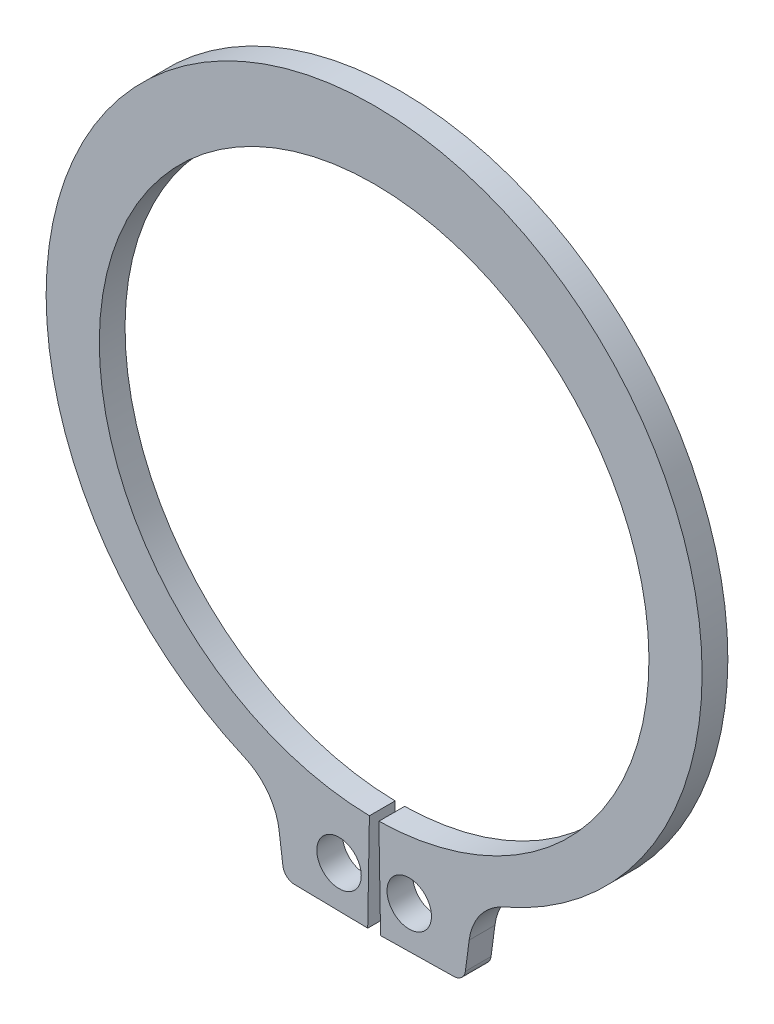
SolidWorks part; units mm, degrees
ref_plane "Plane1" through (0, 0, 0) normal (0, 0, 1) x (1, 0, 0)
ref_plane "Plane2" through (0, 0, 0) normal (0, 1, 0) x (1, 0, 0)
ref_plane "Plane3" through (0, 0, 0) normal (1, 0, 0) x (0, 0, -1)
sketch "Clipboard" plane through (0, 0, 0) normal (0, 0, 1) x (1, 0, 0)
  line L0 (0, 0) -> (2.9, 0)
  line L1 (0, 0) -> (0, 1.7)
  line L2 (0, 0) -> (0, -4.2)
  circle A0 centre (0, 0) radius 0.95
  circle A1 centre (0, 0) radius 12.5
  dimension "HoleDia" = 1.9
  dimension "ShaftDia" = 25
  dimension "LargeSection" = 2.9
  dimension "SmallSection" = 1.7
  dimension "LugSection" = 4.2
sketch "BodySke" plane through (0, 0, 0) normal (0, 0, 1) x (1, 0, 0)
  line L0 (-1.5431, 0) -> (1.5431, 0) construction
  line L1 (0, 0) -> (0, 14.65) construction
  line L2 (0.2026, -11.7483) -> (0.275, -15.9476)
  line L3 (-0.2026, -11.7483) -> (-0.275, -15.9476)
  line L4 (0, 0) -> (6.5413, -14.547) construction
  line L5 (0, 0) -> (-6.5413, -14.547) construction
  line L6 (0.275, -15.9476) -> (3.4129, -15.8935)
  line L7 (4.063, -14.2207) -> (3.9, -15.4589)
  line L8 (-4.063, -14.2207) -> (-3.9, -15.4589)
  line L9 (-0.275, -15.9476) -> (-3.4129, -15.8935)
  circle A0 centre (0, 0) radius 11.75 construction
  arc A1 (0.2026, -11.7483) -> (-0.2026, -11.7483) centre (0, 0) ccw
  arc A2 (5.516, -12.2669) -> (-5.516, -12.2669) centre (0, 0.6264) ccw construction
  arc A3 (0.275, -15.9476) -> (3.9942, -15.4418) centre (0, 0) ccw construction
  arc A4 (5.5517, -12.2515) -> (4.063, -14.2207) centre (6.5413, -14.547) ccw
  arc A5 (-4.063, -14.2207) -> (-5.5517, -12.2515) centre (-6.5413, -14.547) ccw
  arc A6 (-3.9942, -15.4418) -> (-0.275, -15.9476) centre (0, 0) ccw construction
  arc A7 (5.5517, -12.2515) -> (-5.5517, -12.2515) centre (0, 0.6264) ccw
  arc A8 (-4.1437, -13.6081) -> (4.1437, -13.6081) centre (0, 0) ccw construction
  circle A9 centre (1.5, -14.1457) radius 0.95
  circle A10 centre (-1.5, -14.1457) radius 0.95
  arc A11 (3.9, -15.4589) -> (3.4129, -15.8935) centre (3.4043, -15.3936) cw
  arc A12 (-3.9, -15.4589) -> (-3.4129, -15.8935) centre (-3.4043, -15.3936) ccw
  point P28 (3.8991, -15.4661)
  point P31 (-3.8991, -15.4661)
  dimension "GrooveDia" = 23.5
  dimension "LugRad" = 15.95
  dimension "HoleOffsetRad" = 14.225
  dimension "HoleDia" = 1.9
  dimension "D3" = 0.5
  dimension "LargeRad" = 14.65
  dimension "SmallRad" = 13.45
  dimension "SmallAngle" = 48.424
  dimension "D2" = 15
  dimension "HoleSpacing" = 3
  dimension "Gap" = 0.55
extrude "Body" add sketch "BodySke" against normal blind 1.1
sketch "NotSke" plane through (0, 0, 0) normal (0, 0, 1) x (1, 0, 0)
  line L0 (1.5, -13.1957) -> (1.5, -15.0957)
  line L1 (1.5, -15.0957) -> (-1.5, -15.0957)
  line L2 (-1.5, -15.0957) -> (-1.5, -13.1957)
  line L3 (-1.5, -13.1957) -> (1.5, -13.1957)
  circle A0 centre (1.5, -14.1457) radius 0.95 construction
  circle A1 centre (-1.5, -14.1457) radius 0.95 construction
extrude "Notch" [suppressed] cut sketch "NotSke" against normal through all
equation "' \"ShaftDia@Clipboard\" = 4"
equation "' \"Thickness@Body\" = 0.25"
equation "' \"GrooveDia@BodySke\" = 3.8"
equation "' \"LugSection@Clipboard\" = 1.35"
equation "' \"LargeSection@Clipboard\" = 0.65"
equation "' \"SmallSection@Clipboard\" = 0.4"
equation "' \"HoleDia@Clipboard\" = 0.6"
equation "' \"ShaftDia@Clipboard\" = 15"
equation "' \"Thickness@Body\" = 0.9"
equation "' \"GrooveDia@BodySke\" = 14.15"
equation "' \"LugSection@Clipboard\" = 2.8"
equation "' \"LargeSection@Clipboard\" = 1.8"
equation "' \"SmallSection@Clipboard\" = 1.05"
equation "' \"HoleDia@Clipboard\" = 1.2"
equation "\"Gap@BodySke\" =  \"Thickness@Body\" / 2"
equation "\"LargeRad@BodySke\" =  \"GrooveDia@BodySke\" / 2 +  \"LargeSection@Clipboard\""
equation "\"SmallRad@BodySke\" =  \"GrooveDia@BodySke\" / 2 +  \"SmallSection@Clipboard\""
equation "\"LugRad@BodySke\" = \"GrooveDia@BodySke\" / 2 + \"LugSection@Clipboard\""
equation "\"HoleOffsetRad@BodySke\" = (  \"ShaftDia@Clipboard\" / 2 + \"LugRad@BodySke\" ) / 2"
equation "\"HoleSpacing@BodySke\" = \"Gap@BodySke\"  * 2 +  \"HoleDia@Clipboard\""
equation "\"HoleDia@BodySke\" =  \"HoleDia@Clipboard\""
equation "\"SmallAngle@BodySke\" = atn(\"HoleSpacing@BodySke\" / 2 / sqr(\"HoleOffsetRad@BodySke\"  * \"HoleOffsetRad@BodySke\" - (\"HoleSpacing@BodySke\" / 2) * (\"HoleSpacing@BodySke\" / 2) ))  * 8 * ( 180 / 3.141593)"
